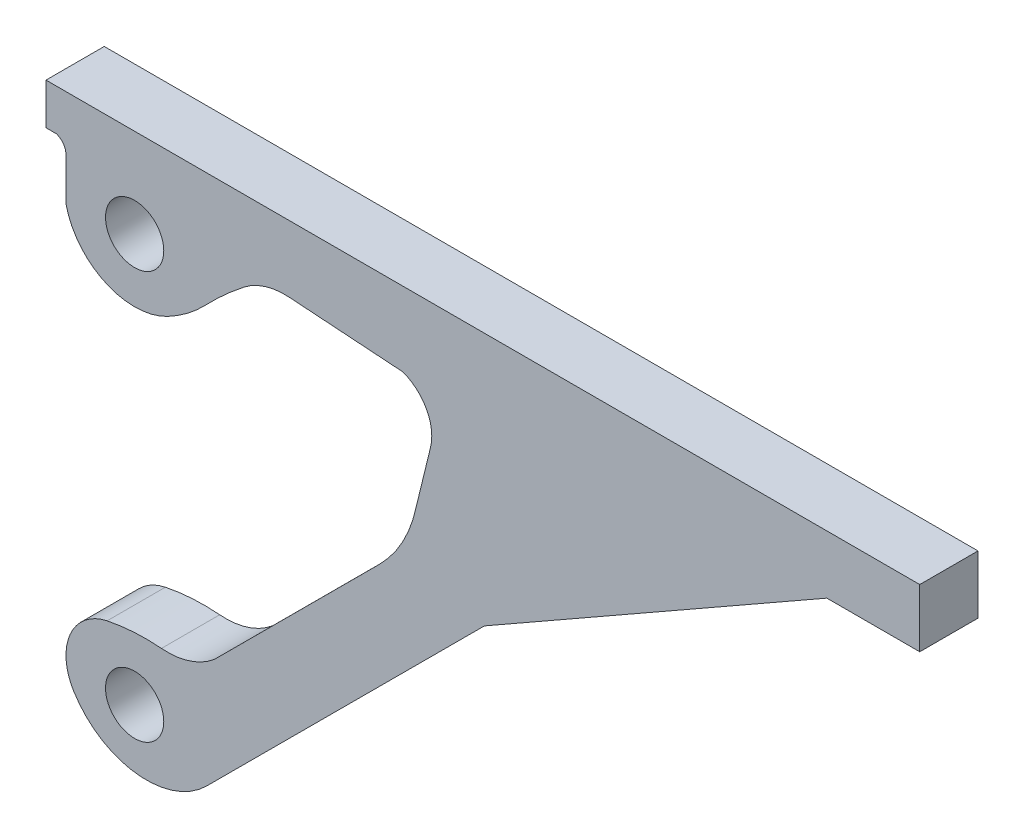
SolidWorks part; units mm, degrees
ref_plane "Front Plane" through (0, 0, 0) normal (0, 0, 1) x (1, 0, 0)
ref_plane "Top Plane" through (0, 0, 0) normal (0, 1, 0) x (1, 0, 0)
ref_plane "Right Plane" through (0, 0, 0) normal (1, 0, 0) x (0, 0, -1)
sketch "Szkic1" [suppressed] plane through (0, 0, 0) normal (0, 0, 1) x (1, 0, 0)
  line L1 (0, 0) -> (300, 0)
  line L2 (0, 0) -> (0, 200)
  line L3 (0, 200) -> (300, 200)
  line L4 (300, 0) -> (300, 200)
  circle A0 centre (30, 170) radius 10
  circle A1 centre (30, 30) radius 10
  dimension "D3" = 20
  dimension "D4" = 30
  dimension "D5" = 30
  dimension "D6" = 30
  dimension "D1" = 200
  dimension "D2" = 300
extrude "Dodanie-wyciągnięcie1" [suppressed] add sketch "Szkic1" along normal blind 20
other "Grafika1" [suppressed]
other "Grafika (Zamknięta) -1" [suppressed]
sketch "Szkic2" plane through (0, 0, 0) normal (0, 0, 1) x (1, 0, 0)
  line L0 (0, 185.8154) -> (0, 200)
  line L1 (0, 200) -> (300, 200)
  line L2 (300, 200) -> (300, 180)
  line L3 (300, 180) -> (268.101, 180)
  line L4 (268.101, 180) -> (150.5377, 112.9687)
  line L5 (150.5377, 112.9687) -> (55.1528, 17.6682)
  line L6 (57.922, 56.7535) -> (114.4855, 113.267)
  line L7 (127.061, 136.4662) -> (132.0253, 156.7626)
  line L8 (122.4618, 174.4916) -> (83.4536, 177.1864)
  line L9 (6.8598, 166.6165) -> (6.8598, 181.2567)
  line L10 (3.5636, 185.8154) -> (0, 185.8154)
  circle A0 centre (30.4314, 29.4435) radius 10
  circle A1 centre (30.4314, 169.4435) radius 10
  arc A2 (55.1528, 17.6682) -> (9.4466, 23.1429) centre (34.4534, 38.386) cw
  arc A3 (9.4466, 23.1429) -> (20.9691, 49.6908) centre (24.5624, 32.3568) cw
  arc A4 (20.9691, 49.6908) -> (39.6347, 50.8259) centre (34.2251, -14.256) cw
  arc A5 (39.6347, 50.8259) -> (57.922, 56.7535) centre (41.697, 75.6365) ccw
  arc A6 (114.4855, 113.267) -> (127.061, 136.4662) centre (81.7758, 146.0057) ccw
  arc A7 (132.0253, 156.7626) -> (122.4618, 174.4916) centre (117.4287, 160.3328) ccw
  arc A8 (83.4536, 177.1864) -> (67.9799, 172.4275) centre (81.9003, 154.7005) ccw
  arc A9 (67.9799, 172.4275) -> (54.6413, 160.3328) centre (146.5314, 72.3958) ccw
  arc A10 (54.6413, 160.3328) -> (41.697, 150.5709) centre (18.1591, 195.2456) cw
  arc A11 (41.697, 150.5709) -> (6.8598, 166.6165) centre (30.4314, 171.9528) cw
  arc A12 (6.8598, 181.2567) -> (3.5636, 185.8154) centre (2.0593, 181.2567) ccw
  point P43 (0, 0)
  point P44 (30.4314, 169.4435)
  dimension "D1" = 140
extrude "Dodanie-wyciągnięcie2" add sketch "Szkic2" along normal blind 20
